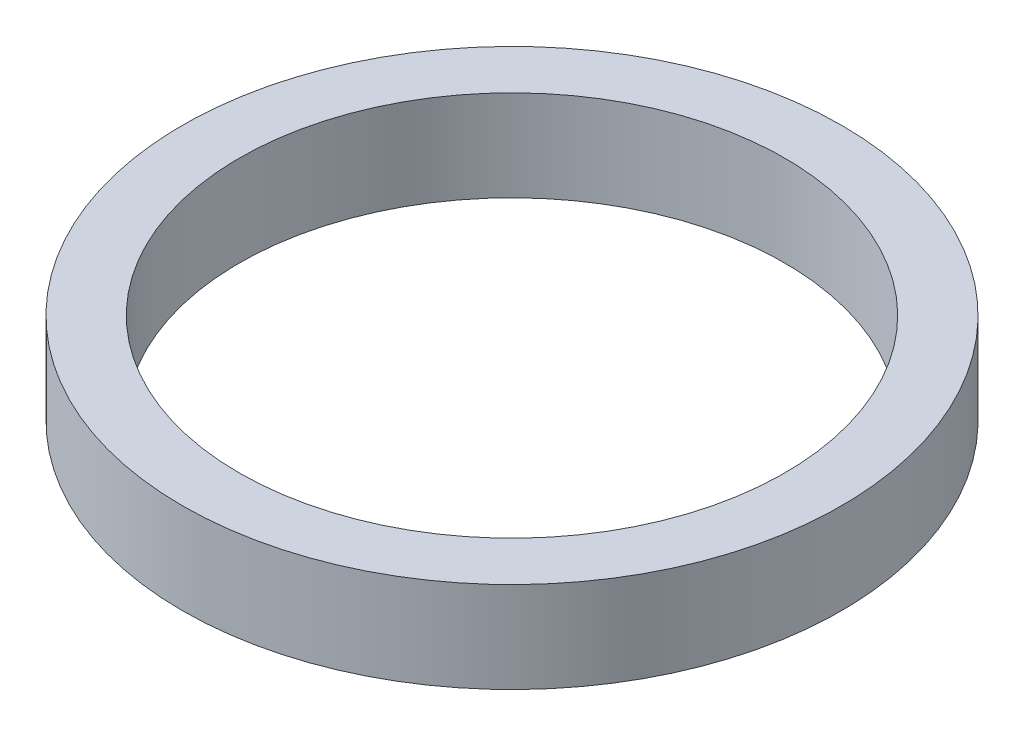
SolidWorks part; units mm, degrees
ref_plane "Front Plane" through (0, 0, 0) normal (0, 0, 1) x (1, 0, 0)
ref_plane "Top Plane" through (0, 0, 0) normal (0, 1, 0) x (1, 0, 0)
ref_plane "Right Plane" through (0, 0, 0) normal (1, 0, 0) x (0, 0, -1)
sketch "Sketch1" plane through (0, 0, 0) normal (0, 1, 0) x (1, 0, 0)
  circle A0 centre (0, 0) radius 3
  circle A1 centre (0, 0) radius 3.625
  dimension "D1" = 6
  dimension "D2" = 7.25
extrude "Boss-Extrude1" add sketch "Sketch1" along normal blind 1
